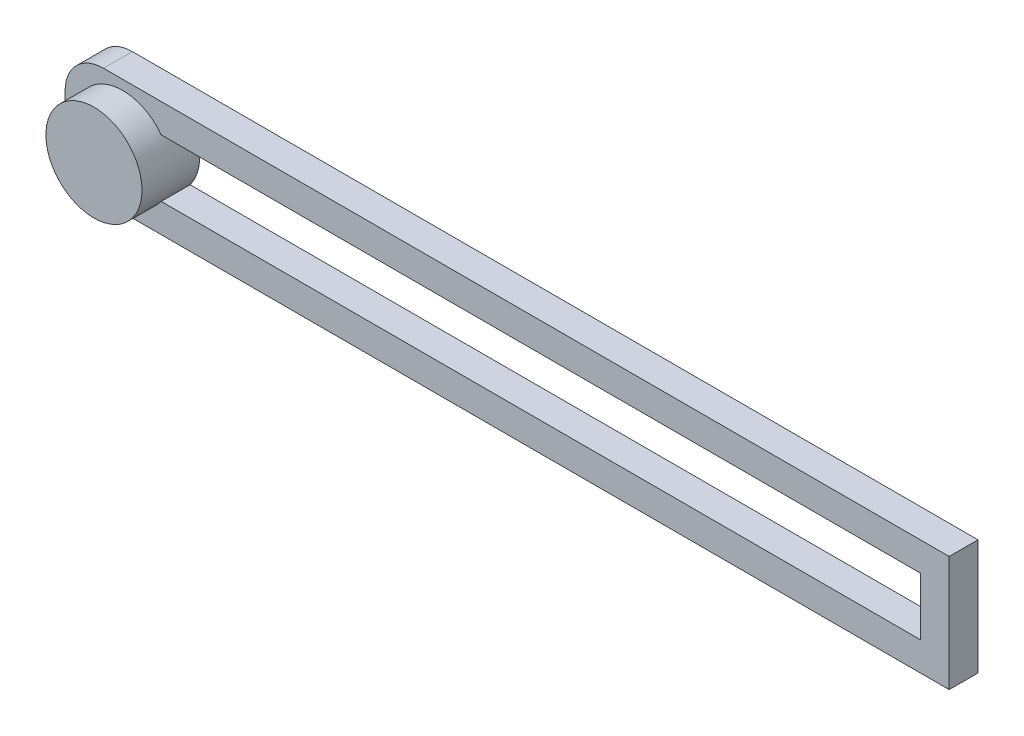
SolidWorks part; units mm, degrees
ref_plane "Front Plane" through (0, 0, 0) normal (0, 0, 1) x (1, 0, 0)
ref_plane "Top Plane" through (0, 0, 0) normal (0, 1, 0) x (1, 0, 0)
ref_plane "Right Plane" through (0, 0, 0) normal (1, 0, 0) x (0, 0, -1)
sketch "Sketch1" plane through (0, 0, 0) normal (0, 0, 1) x (1, 0, 0)
  line L1 (-46, -6) -> (46, -6)
  line L2 (-46, -6) -> (-46, 6)
  line L3 (-46, 6) -> (46, 6)
  line L4 (46, -6) -> (46, 6)
  line L5 (-46, -6) -> (46, 6) construction
  line L6 (-46, 6) -> (46, -6) construction
  point P0 (0, 0)
  dimension "D1" = 12
  dimension "D2" = 92
extrude "Boss-Extrude1" add sketch "Sketch1" along normal blind 3
fillet "Fillet1" radius 4 2 edges at (-46, -6, 1.5) (-46, 6, 1.5)
sketch "Sketch2" plane through (0, 0, 3) normal (0, 0, 1) x (1, 0, 0)
  line L8 (-43, 2) -> (-43, -2)
  line L9 (-42, -3) -> (43, -3)
  line L10 (43, -3) -> (43, 3)
  line L11 (43, 3) -> (-42, 3)
  line L12 (-43, 2) -> (-43, -2)
  line L13 (-42, -3) -> (43, -3)
  line L14 (43, -3) -> (43, 3)
  line L15 (43, 3) -> (-42, 3)
  arc A4 (-43, -2) -> (-42, -3) centre (-42, -2) ccw
  arc A5 (-42, 3) -> (-43, 2) centre (-42, 2) ccw
  arc A6 (-43, -2) -> (-42, -3) centre (-42, -2) ccw
  arc A7 (-42, 3) -> (-43, 2) centre (-42, 2) ccw
  dimension "D1" = 3
extrude "Cut-Extrude1" cut sketch "Sketch2" against normal blind 3
sketch "Sketch3" plane through (0, 0, 3) normal (0, 0, 1) x (1, 0, 0)
  line L0 (-46, 0) -> (-40, 0) construction
  line L1 (-46, 2) -> (-46, -2) construction
  circle A0 centre (-40, 0) radius 5
  dimension "D1" = 10
  dimension "D2" = 6
extrude "Boss-Extrude2" add sketch "Sketch3" along normal blind 3 and the other way up to surface (3 mm away) other way up to face at (-14.069, 0, 0)
